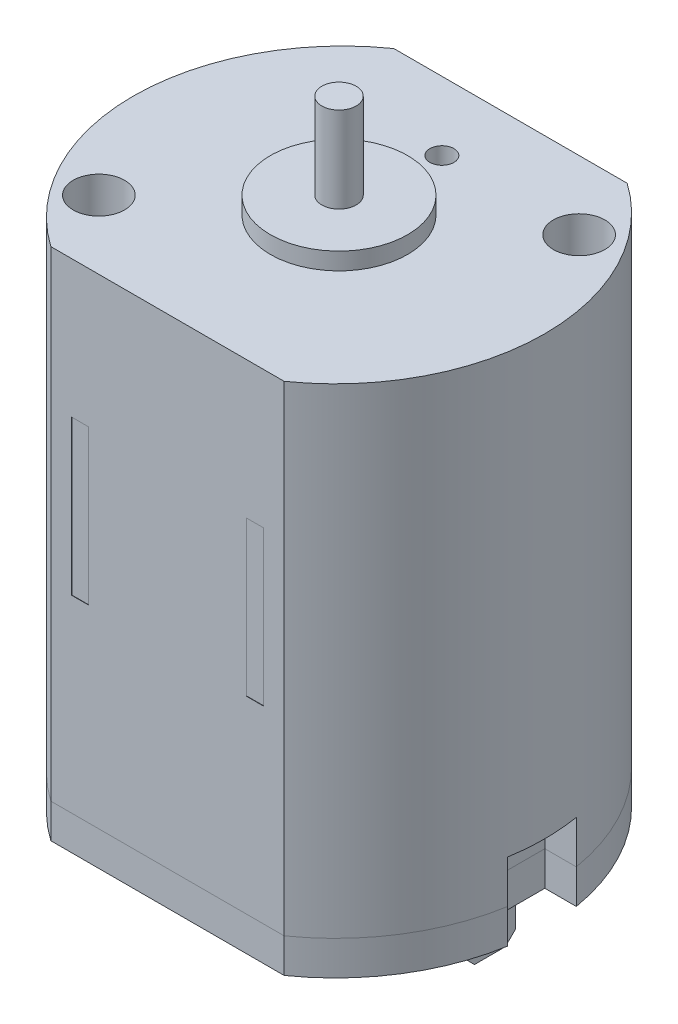
SolidWorks part; units mm, degrees
ref_plane "Alzado" through (0, 0, 0) normal (0, 0, 1) x (1, 0, 0)
ref_plane "Planta" through (0, 0, 0) normal (0, 1, 0) x (1, 0, 0)
ref_plane "Vista lateral" through (0, 0, 0) normal (1, 0, 0) x (0, 0, -1)
sketch "Croquis1" plane through (0, 0, 0) normal (0, 1, 0) x (1, 0, 0)
  line L0 (0, 0) -> (0, 6.858) construction
  line L1 (-3.4, 5) -> (3.4, 5)
  line L2 (0, 0) -> (6, 0) construction
  line L4 (-3.4, -5) -> (3.4, -5)
  arc A0 (3.4, 5) -> (3.4, -5) centre (-0.1077, 0) cw
  arc A1 (-3.4, 5) -> (-3.4, -5) centre (0.1077, 0) ccw
  point P11 (0, -5)
  point P13 (0, 5)
  dimension "D1" = 3.4
  dimension "D2" = 5
extrude "Saliente-Extruir1" add sketch "Croquis1" along normal blind 1
sketch "Croquis2" plane through (0, 1, 0) normal (0, 1, 0) x (1, 0, 0)
  line L0 (-3.4, 5) -> (3.4, 5)
  line L2 (3.4, -5) -> (-3.4, -5)
  arc A0 (-3.4, 5) -> (-3.4, -5) centre (0.1077, 0) ccw
  arc A1 (3.4, 5) -> (3.4, -5) centre (-0.1077, 0) cw
extrude "Saliente-Extruir2" add sketch "Croquis2" along normal blind 14 separate body
sketch "Croquis3" plane through (0, 0, 5) normal (0, 0, 1) x (1, 0, 0)
  line L0 (-2.8, 11) -> (-2.8, 6.5)
  line L1 (-2.8, 6.5) -> (-2.3, 6.5)
  line L2 (-2.3, 6.5) -> (-2.3, 11)
  line L3 (-2.3, 11) -> (-2.8, 11)
  line L4 (0, 1) -> (0, 14.4283) construction
  line L5 (-3.4, 1) -> (3.4, 1) construction
  line L6 (-3.4, 1) -> (3.4, 1) construction
  line L7 (-3.4, 15) -> (-3.4, 1) construction
  line L8 (2.3, 6.5) -> (2.3, 11)
  line L9 (2.8, 6.5) -> (2.3, 6.5)
  line L10 (2.8, 11) -> (2.8, 6.5)
  line L11 (2.3, 11) -> (2.8, 11)
  dimension "D1" = 0.5
  dimension "D2" = 5.5
  dimension "D3" = 4.5
  dimension "D4" = 0.6
extrude "Cortar-Extruir1" cut sketch "Croquis3" against normal blind 0.01
mirror "Simetría2" about plane through (0, 0, 0) normal (0, 0, 1) of "Cortar-Extruir1"
sketch "Croquis4" plane through (0, 0, 0) normal (0, -1, 0) x (1, 0, 0)
  line L0 (0, 0) -> (0, 5) construction
  line L1 (-3.4, 5) -> (3.4, 5) construction
  line L2 (0, 0) -> (6, 0) construction
  line L3 (5, 1) -> (5, -1)
  line L4 (-5, 1) -> (-5.9176, 1)
  line L5 (5, 1) -> (5.9176, 1)
  line L6 (5, -1) -> (5.9176, -1)
  line L7 (-5, 1) -> (-5, -1)
  line L8 (-5, -1) -> (-5.9176, -1)
  arc A0 (3.4, -5) -> (3.4, 5) centre (-0.1077, 0) ccw construction
  arc A1 (5.9176, 1) -> (5.9176, -1) centre (-0.1077, 0) cw
  arc A2 (-5.9176, 1) -> (-5.9176, -1) centre (0.1077, 0) ccw
  point P14 (5, 0)
  dimension "D2" = 1
extrude "Cortar-Extruir2" cut sketch "Croquis4" against normal blind 2.25
sketch "Croquis5" plane through (0, 0, 0) normal (0, -1, 0) x (1, 0, 0)
  circle A0 centre (0, 0) radius 2.5
  dimension "D1" = 5
extrude "Saliente-Extruir3" add sketch "Croquis5" along normal blind 1
sketch "Croquis6" plane through (0, -1, 0) normal (0, -1, 0) x (1, 0, 0)
  circle A0 centre (0, 0) radius 1
  dimension "D1" = 2
extrude "Cortar-Extruir3" cut sketch "Croquis6" against normal blind 0.5
sketch "Croquis7" plane through (0, 0, 0) normal (0, -1, 0) x (1, 0, 0)
  line L0 (0, 0) -> (0, 5) construction
  line L1 (-3.4, 5) -> (3.4, 5) construction
  line L2 (4.4, 0.75) -> (4.4, -0.75)
  line L4 (4.4, 0.75) -> (4.1, 0.75)
  line L5 (4.1, 0.75) -> (4.1, -0.75)
  line L6 (4.1, -0.75) -> (4.4, -0.75)
  line L7 (-4.1, 0.75) -> (-4.1, -0.75)
  line L8 (-4.4, 0.75) -> (-4.1, 0.75)
  line L9 (-4.4, 0.75) -> (-4.4, -0.75)
  line L10 (-4.1, -0.75) -> (-4.4, -0.75)
  dimension "D1" = 1.5
  dimension "D3" = 0.3
extrude "Saliente-Extruir4" add sketch "Croquis7" along normal blind 1.5
sketch "Croquis8" plane through (4.4, 0, 0) normal (1, 0, 0) x (0, 0, -1)
  line L0 (0.75, -1.5) -> (0.75, 0) construction
  circle A0 centre (0, -0.75) radius 0.5
  point P4 (0.75, -0.75)
  dimension "D1" = 1
extrude "Cortar-Extruir4" cut sketch "Croquis8" against normal blind 1
mirror "Simetría3" about plane through (0, 0, 0) normal (1, 0, 0) of "Cortar-Extruir4"
chamfer "Chaflán1" distance 0.3 angle 45 4 edges at (4.25, -1.5, -0.75) (4.25, -1.5, 0.75) (-4.25, -1.5, 0.75) (-4.25, -1.5, -0.75)
sketch "Croquis9" plane through (0, 0, 0) normal (0, -1, 0) x (1, 0, 0)
  circle A0 centre (2.6891, 3.0864) radius 0.75
  circle A1 centre (0, -3.6609) radius 0.75
  dimension "D1" = 1.5
  dimension "D2" = 1.5
extrude "Cortar-Extruir5" cut sketch "Croquis9" against normal blind 0.05
sketch "Croquis10" plane through (0, 0.05, 0) normal (0, -1, 0) x (1, 0, 0)
  circle A0 centre (2.6891, 3.0864) radius 0.25
  dimension "D1" = 0.5
extrude "Cortar-Extruir6" cut sketch "Croquis10" against normal blind 1
sketch "Croquis11" plane through (0, 0, 0) normal (0, -1, 0) x (1, 0, 0)
  line L0 (0, 5) -> (0, 2.3408) construction
  line L1 (-3.4, 5) -> (3.4, 5) construction
  line L2 (-2.6874, 3.8364) -> (-2.6874, 3.0864) construction
  line L3 (-2.6874, 3.0864) -> (-1.9374, 3.0864) construction
  line L4 (-2.6374, 3.7948) -> (-2.6374, 3.1364)
  line L5 (-2.6374, 3.1364) -> (-1.9718, 3.1364)
  line L6 (-2.6374, 3.7948) -> (-2.6374, 3.802)
  line L7 (-2.6374, 3.0364) -> (-1.9718, 3.0364)
  line L8 (-2.6374, 2.378) -> (-2.6374, 3.0364)
  line L9 (-2.7374, 2.378) -> (-2.7374, 3.0364)
  line L10 (-2.7374, 3.0364) -> (-3.403, 3.0364)
  line L11 (-2.7374, 3.1364) -> (-3.403, 3.1364)
  line L12 (-2.7374, 3.7948) -> (-2.7374, 3.1364)
  line L13 (-2.7374, 2.378) -> (-2.7374, 2.3708)
  line L14 (-2.6374, 2.378) -> (-2.6374, 2.3708)
  line L15 (-2.7374, 3.7948) -> (-2.7374, 3.802)
  circle A1 centre (-2.6874, 3.0864) radius 0.75
  arc A2 (-2.6374, 3.802) -> (-2.7374, 3.802) centre (-2.6874, 3.0864) ccw
  arc A4 (-1.9718, 3.0364) -> (-1.9718, 3.1364) centre (-2.6874, 3.0864) ccw
  arc A5 (-2.7374, 2.3708) -> (-2.6374, 2.3708) centre (-2.6874, 3.0864) ccw
  arc A6 (-3.403, 3.1364) -> (-3.403, 3.0364) centre (-2.6874, 3.0864) ccw
  dimension "D1" = 0.05
  dimension "D2" = 0.05
extrude "Cortar-Extruir7" cut sketch "Croquis11" against normal blind 0.05
sketch "Croquis12" plane through (0, 15, 0) normal (0, 1, 0) x (1, 0, 0)
  circle A0 centre (0, 0) radius 2
  dimension "D1" = 4
extrude "Saliente-Extruir5" add sketch "Croquis12" along normal blind 0.5 separate body
sketch "Croquis13" plane through (0, 15.5, 0) normal (0, 1, 0) x (1, 0, 0)
  circle A0 centre (0, 0) radius 0.5
  dimension "D1" = 1
extrude "Saliente-Extruir6" add sketch "Croquis13" along normal blind 2.5 separate body
sketch "Croquis14" plane through (0, 15, 0) normal (0, 1, 0) x (1, 0, 0)
  line L0 (0, 0) -> (0, -5) construction
  line L1 (-3.4, -5) -> (3.4, -5) construction
  line L2 (0, 0) -> (3.9829, 0) construction
  circle A1 centre (-4, -3) radius 0.75
  circle A4 centre (4, 3) radius 0.75
  circle A5 centre (0, 3) radius 0.35
  dimension "D3" = 1.5
  dimension "D4" = 2
extrude "Cortar-Extruir8" cut sketch "Croquis14" against normal blind 2.5
